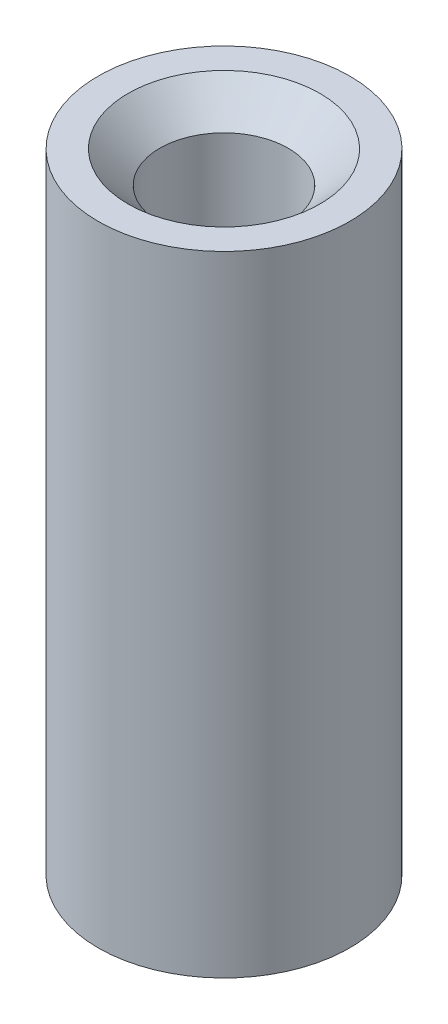
SolidWorks part; units mm, degrees
ref_plane "Front Plane" through (0, 0, 0) normal (0, 0, 1) x (1, 0, 0)
ref_plane "Top Plane" through (0, 0, 0) normal (0, 1, 0) x (1, 0, 0)
ref_plane "Right Plane" through (0, 0, 0) normal (1, 0, 0) x (0, 0, -1)
sketch "Sketch1" plane through (0, 0, 0) normal (0, 1, 0) x (1, 0, 0)
  circle A0 centre (0, 0) radius 5
  dimension "D1" = 10
extrude "Boss-Extrude1" add sketch "Sketch1" against normal blind 25
hole_wizard "1/4-20 Tapped Hole1" positions "Sketch2" profile "Sketch4" tap size "1/4-20" standard "ANSI Inch" end condition through all
sketch "Sketch2" plane through (0, 0, 0) normal (0, 1, 0) x (1, 0, 0)
  point P0 (0, 0)
sketch "Sketch4" plane through (0, 0, 0) normal (1, 0, 0) x (0, 0, 1)
  line L0 (0, 0) -> (0, 25)
  line L1 (0, 25) -> (2.5527, 25)
  line L2 (2.5527, 25) -> (2.5527, 1.2573)
  line L3 (2.5527, 1.2573) -> (3.81, 0)
  line L5 (3.81, 0) -> (0, 0)
  line L6 (-2.5527, 1.2573) -> (-3.81, 0) construction
  line L11 (0, -6.35) -> (0, 107.95) construction
  dimension "Thru Tap Drill Dia." = 5.1054
  dimension "Thru Tap Drill Depth" = 25
  dimension "Near C'Sink Dia." = 7.62
  dimension "Near C'Sink Angle" = 90
cosmetic thread "Hole Thread1" parameters "D2"=6.35
